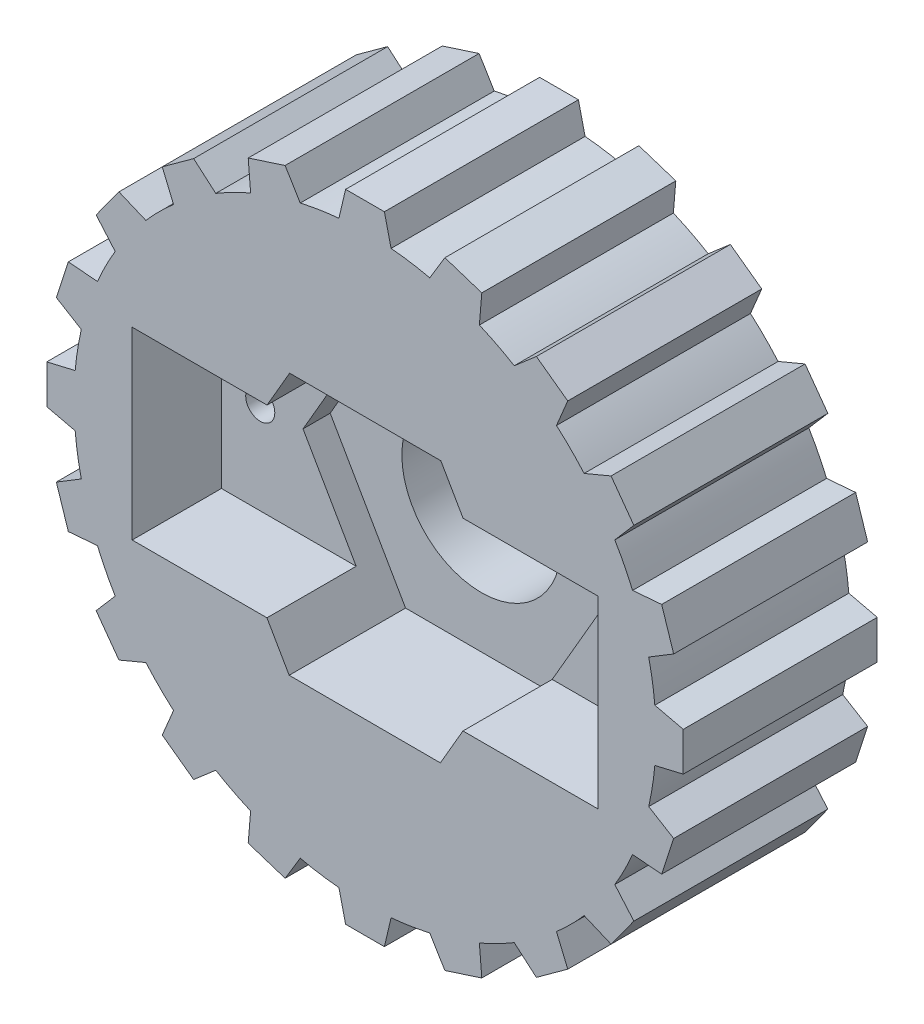
SolidWorks part; units mm, degrees
ref_plane "Front Plane" through (0, 0, 0) normal (0, 0, 1) x (1, 0, 0)
ref_plane "Top Plane" through (0, 0, 0) normal (0, 1, 0) x (1, 0, 0)
ref_plane "Right Plane" through (0, 0, 0) normal (1, 0, 0) x (0, 0, -1)
sketch "Sketch1" plane through (0, 0, 0) normal (0, 0, 1) x (1, 0, 0)
  circle A0 centre (0, 0) radius 15
  dimension "D1" = 30
extrude "Extrude1" add sketch "Sketch1" along normal blind 10
sketch "Sketch2" plane through (0, 0, 10) normal (0, 0, 1) x (1, 0, 0)
  line L0 (1.4, 14.7045) -> (1, 16.4045)
  line L1 (1, 16.4045) -> (-1, 16.4045)
  line L2 (-1, 16.4045) -> (-1.4, 14.7045)
  line L3 (-1.4, 14.7045) -> (1.4, 14.7045)
  line L4 (0, 0) -> (0, 39.164) construction
  point P7 (0, 14.7045)
  point P8 (0, 16.4045)
  dimension "D1" = 2.8
  dimension "D2" = 2
  dimension "D3" = 1.7
extrude "Extrude3" add sketch "Sketch2" against normal up to surface (10 mm away) up to face at (15, 0, 0)
pattern_circular "CirPattern1" count 20 every 18 about axis through (0, 0, 0) along (0, 0, 1) of "Extrude3"
hole_wizard "Ø8.2 (8.2) Diameter Hole1" positions "3DSketch1" profile "Sketch3" hole size "Ø8.2" standard "Ansi Metric"
sketch3d "3DSketch1"
  point P4 (0, 0, 0)
sketch "Sketch3" plane through (0, 0, 0) normal (1, 0, 0) x (0, 1, 0)
  line L0 (0, 0) -> (0, 12.4635)
  line L1 (0, 12.4635) -> (4.1, 10)
  line L2 (4.1, 10) -> (4.1, 0)
  line L5 (4.1, 0) -> (0, 0)
  line L10 (0, 12.4635) -> (-4.1, 10) construction
  line L11 (0, -6.35) -> (0, 107.95) construction
  dimension "Hole Dia." = 8.2
  dimension "Hole Depth" = 10
  dimension "Drill Angle" = 118
sketch "Sketch4" plane through (0, 0, 10) normal (0, 0, 1) x (1, 0, 0)
  line L0 (0, 0) -> (0, 12.1662) construction
  line L1 (12, -4.75) -> (-12, -4.75)
  line L2 (12, -4.75) -> (12, 4.75)
  line L3 (12, 4.75) -> (-12, 4.75)
  line L4 (-12, -4.75) -> (-12, 4.75)
  point P4 (0, 4.75)
  point P8 (12, 0)
  dimension "D1" = 24
  dimension "D2" = 9.5
extrude "Extrude4" cut sketch "Sketch4" against normal blind 4.6
hole_wizard "Ø1.5 (1.5) Diameter Hole1" positions "3DSketch2" profile "Sketch5" hole size "Ø1.5" standard "Ansi Metric"
sketch3d "3DSketch2"
  line L1 (10, 0, 0) -> (0, 0, 0) construction
  line L3 (0, 0, 0) -> (-10, 0, 0) construction
  point P0 (10, 0, 0)
  point P2 (-10, 0, 0)
  dimension "D1" = 20
sketch "Sketch5" plane through (10, 0, 0) normal (1, 0, 0) x (0, 1, 0)
  line L0 (0, 0) -> (0, 150.4506)
  line L1 (0, 150.4506) -> (0.75, 150)
  line L2 (0.75, 150) -> (0.75, 0)
  line L5 (0.75, 0) -> (0, 0)
  line L10 (0, 150.4506) -> (-0.75, 150) construction
  line L11 (0, -6.35) -> (0, 107.95) construction
  dimension "Hole Dia." = 1.5
  dimension "Hole Depth" = 150
  dimension "Drill Angle" = 118
sketch "Sketch6" plane through (0, 0, 10) normal (0, 0, 1) x (1, 0, 0)
  line L1 (3.909, 6.7431) -> (-3.8852, 6.7568)
  line L2 (-3.8852, 6.7568) -> (-7.7942, 0.0137)
  line L3 (-7.7942, 0.0137) -> (-3.909, -6.7431)
  line L4 (-3.909, -6.7431) -> (3.8852, -6.7568)
  line L5 (3.8852, -6.7568) -> (7.7942, -0.0137)
  line L6 (7.7942, -0.0137) -> (3.909, 6.7431)
  circle A1 centre (0, 0) radius 6.75 construction
  dimension "D1" = 13.5
extrude "Extrude5" cut sketch "Sketch6" against normal blind 6
